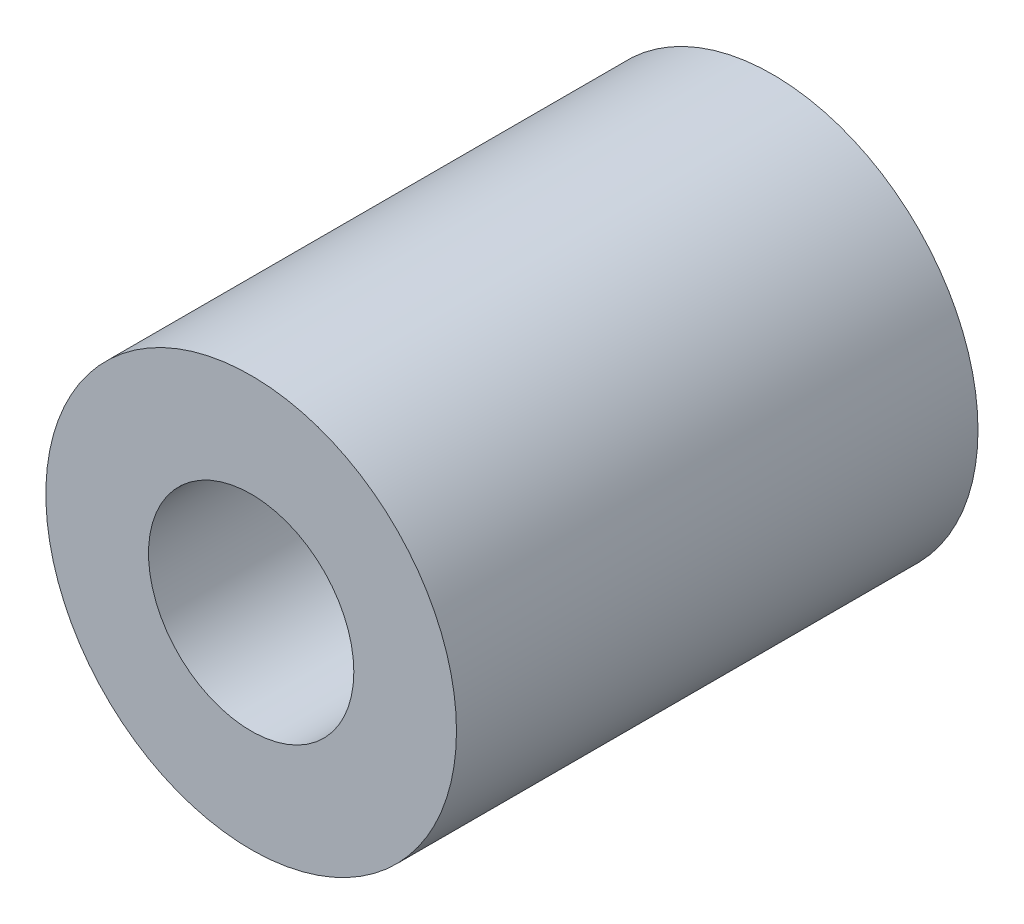
SolidWorks part; units mm, degrees
ref_plane "Front Plane" through (0, 0, 0) normal (0, 0, 1) x (1, 0, 0)
ref_plane "Top Plane" through (0, 0, 0) normal (0, 1, 0) x (1, 0, 0)
ref_plane "Right Plane" through (0, 0, 0) normal (1, 0, 0) x (0, 0, -1)
sketch "Sketch1" plane through (0, 0, 0) normal (0, 0, 1) x (1, 0, 0)
  circle A0 centre (0, 0) radius 5
  dimension "D1" = 10
extrude "Boss-Extrude1" add sketch "Sketch1" along normal blind 12.7
hole_wizard "Ø5.0mm Dowel Hole1" positions "Sketch2" profile "Sketch3" hole size "Ø5.0" standard "ANSI Metric" end condition up to next
sketch "Sketch2" plane through (0, 0, 12.7) normal (0, 0, 1) x (1, 0, 0)
  point P0 (0, 0)
sketch "Sketch3" plane through (0, 0, 12.7) normal (1, 0, 0) x (0, -1, 0)
  line L0 (0, 0) -> (0, 12.7)
  line L1 (0, 12.7) -> (2.5, 12.7)
  line L2 (2.5, 12.7) -> (2.5, 0)
  line L5 (2.5, 0) -> (0, 0)
  line L11 (0, -6.35) -> (0, 107.95) construction
  dimension "Thru Hole Dia." = 5
  dimension "Thru Hole Depth" = 12.7
